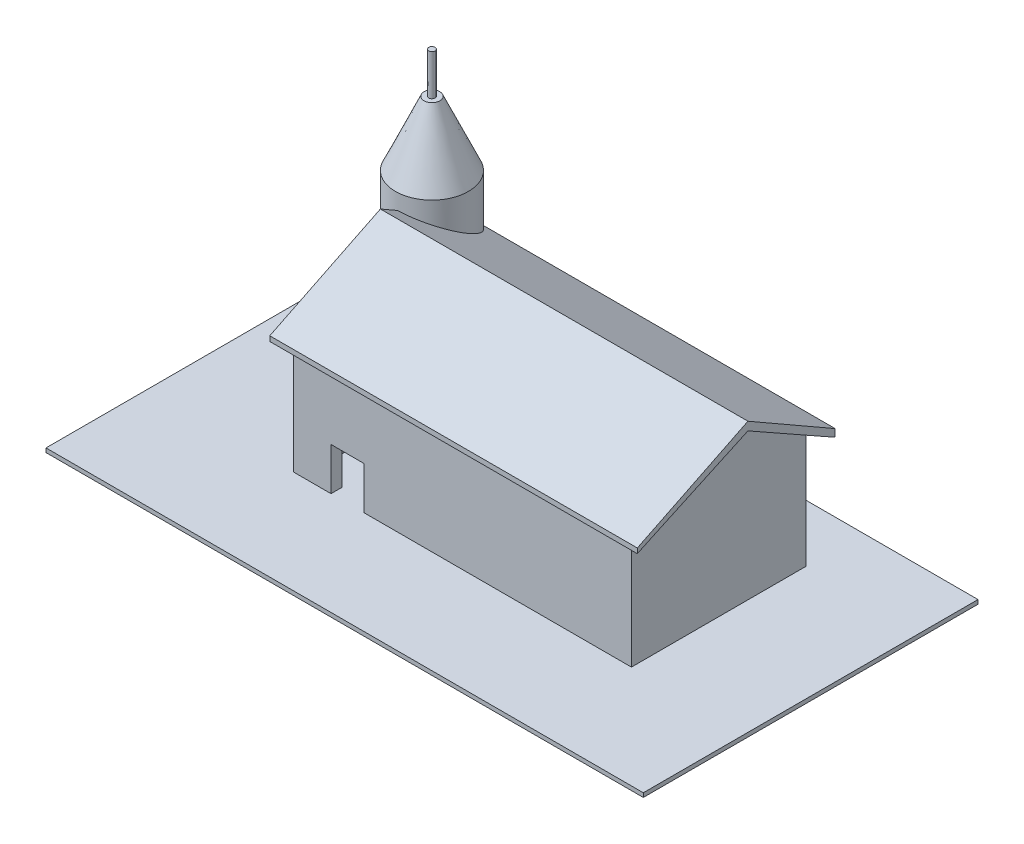
SolidWorks part; units mm, degrees
ref_plane "Front Plane" through (0, 0, 0) normal (0, 0, 1) x (1, 0, 0)
ref_plane "Top Plane" through (0, 0, 0) normal (0, 1, 0) x (1, 0, 0)
ref_plane "Right Plane" through (0, 0, 0) normal (1, 0, 0) x (0, 0, -1)
sketch "Sketch1" plane through (0, 0, 0) normal (0, 1, 0) x (1, 0, 0)
  line L0 (-68.8725, 45.6485) -> (-68.8725, -36.3058)
  line L1 (-68.8725, -36.3058) -> (77.3873, -36.3058)
  line L2 (77.3873, -36.3058) -> (77.3873, 45.6485)
  line L3 (77.3873, 45.6485) -> (-68.8725, 45.6485)
  point P4 (-68.8725, 47.396)
extrude "Boss-Extrude1" add sketch "Sketch1" along normal blind 1
sketch "Sketch2" plane through (0, 1, 0) normal (0, 1, 0) x (1, 0, 0)
  line L2 (49.2894, 31.6153) -> (49.2894, -11.1177)
  line L3 (49.2894, -11.1177) -> (-33.4668, -11.1177)
  line L4 (-29.6658, 31.6153) -> (49.2894, 31.6153)
  line L5 (-33.4668, -11.1177) -> (-33.4668, 17.015)
  line L6 (-31.3849, 21.9956) -> (-31.3849, -8.3801)
  line L7 (-31.3849, -8.3801) -> (47.0747, -8.3801)
  line L8 (47.0747, -8.3801) -> (47.0747, 28.5963)
  line L9 (47.0747, 28.5963) -> (-31.0863, 28.5963)
  arc A1 (-29.6658, 31.6153) -> (-33.4668, 17.015) centre (-36.1955, 25.5203) ccw
  arc A2 (-31.0863, 28.5963) -> (-31.3849, 21.9956) centre (-36.1955, 25.5203) ccw
  point P11 (-31.0863, 21.9956)
extrude "Boss-Extrude3" add sketch "Sketch2" along normal blind 30
sketch "Sketch3" plane through (0, 31, 0) normal (0, 1, 0) x (1, 0, 0)
  circle A0 centre (-36.1955, 25.5203) radius 8.9323
  arc A1 (-29.6658, 31.6153) -> (-33.4668, 17.015) centre (-36.1955, 25.5203) ccw construction
extrude "Boss-Extrude4" add sketch "Sketch3" along normal blind 30
chamfer "Chamfer2" distance 7 angle 66 1 edges at (-36.1955, 61, -16.588)
sketch "Sketch5" plane through (0, 61, 0) normal (0, 1, 0) x (1, 0, 0)
  circle A0 centre (-36.1955, 25.5203) radius 0.7658
extrude "Boss-Extrude5" add sketch "Sketch5" along normal blind 10
sketch "Sketch7" plane through (49.2894, 0, 0) normal (1, 0, 0) x (0, 0, -1)
  line L0 (-11.1177, 31) -> (12.4116, 41.8358)
  line L1 (12.4116, 41.8358) -> (31.6153, 31)
  line L6 (-11.1177, 31) -> (31.6153, 31)
extrude "Boss-Extrude10" add sketch "Sketch7" against normal up to surface (82.7562 mm away) up to face at (-33.4668, 16, -2.9486)
sketch "Sketch8" plane through (49.2894, 0, 0) normal (1, 0, 0) x (0, 0, -1)
  line L0 (-11.1177, 31) -> (12.4116, 41.8358)
  line L1 (12.4116, 41.8358) -> (31.6153, 31)
  line L2 (31.6153, 31) -> (33.7737, 29.8491)
  line L4 (33.7737, 29.8491) -> (33.7737, 31.6385)
  line L5 (33.7737, 31.6385) -> (12.4116, 43.8822)
  line L6 (12.4116, 43.8822) -> (-14.6728, 30.5456)
  line L7 (-14.6728, 30.5456) -> (-14.6728, 29.3306)
  line L8 (-11.1177, 31) -> (-14.6728, 29.3306)
extrude "Boss-Extrude11" add sketch "Sketch8" against normal blind 85 and the other way blind 5
sketch "Sketch9" plane through (0, 0, 11.1177) normal (0, 0, 1) x (1, 0, 0)
  line L0 (-24.2703, 1) -> (-16.2506, 1)
  line L1 (-33.4668, 1) -> (49.2894, 1) construction
  line L2 (-16.2506, 1) -> (-16.2506, 11.4396)
  line L3 (-16.2506, 11.4396) -> (-24.2703, 11.4396)
  line L4 (-24.2703, 11.4396) -> (-24.2703, 1)
extrude "Cut-Extrude1" cut sketch "Sketch9" against normal up to next
